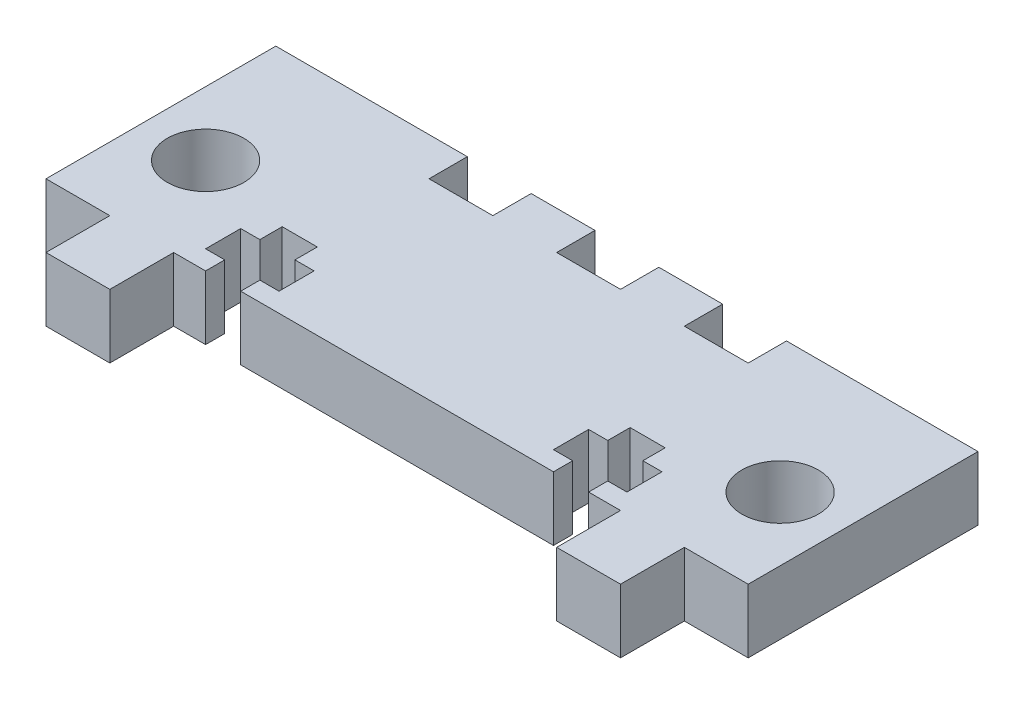
SolidWorks part; units mm, degrees
material "Balsa"
ref_plane "Plan de face" through (0, 0, 0) normal (0, 0, 1) x (1, 0, 0)
ref_plane "Plan de dessus" through (0, 0, 0) normal (0, 1, 0) x (1, 0, 0)
ref_plane "Plan de droite" through (0, 0, 0) normal (1, 0, 0) x (0, 0, -1)
sketch "Esquisse1" plane through (0, 0, 0) normal (0, 1, 0) x (1, 0, 0)
  line L1 (-27.5, 15.5) -> (27.5, 15.5)
  line L2 (-27.5, 15.5) -> (-27.5, -7.5)
  line L3 (-27.5, -7.5) -> (27.5, -7.5)
  line L4 (27.5, 15.5) -> (27.5, -7.5)
  dimension "D1" = 23
  dimension "D2" = 55
  dimension "D3" = 27.5
  dimension "D4" = 7.5
extrude "Boss.-Extru.1" add sketch "Esquisse1" along normal blind 5
sketch "Esquisse2" plane through (0, 5, 0) normal (0, 1, 0) x (1, 0, 0)
  line L1 (27.5, 15.5) -> (-27.5, 15.5) construction
  circle A0 centre (-22.5, 5) radius 3
  circle A1 centre (22.5, 5) radius 3
  dimension "D1" = 6
  dimension "D2" = 6
  dimension "D3" = 45
  dimension "D4" = 22.5
  dimension "D5" = 10.5
extrude "Enlèv. mat.-Extru.1" cut sketch "Esquisse2" against normal blind 5
sketch "Esquisse4" plane through (0, 5, 0) normal (0, 1, 0) x (1, 0, 0)
  line L0 (-15, 3.5) -> (-15, 1.75)
  line L1 (-27.5, -7.5) -> (27.5, -7.5) construction
  line L2 (-15, 1.75) -> (-16.5, 1.75)
  line L3 (-16.5, 1.75) -> (-16.5, -1)
  line L4 (-16.5, -1) -> (-15, -1)
  line L5 (-15, -1) -> (-15, -2.5)
  line L6 (-15, -2.5) -> (-12.25, -2.5)
  line L7 (-12.25, -2.5) -> (-12.25, -1)
  line L8 (-12.25, -1) -> (-10.75, -1)
  line L9 (-10.75, -1) -> (-10.75, 1.75)
  line L10 (-10.75, 1.75) -> (-12.25, 1.75)
  line L11 (-12.25, 1.75) -> (-12.25, 3.5)
  line L12 (-12.25, 3.5) -> (-15, 3.5)
  line L13 (-27.5, 15.5) -> (-27.5, -7.5) construction
  line L14 (0, -4.1132) -> (0, 9.935) construction
  line L15 (12.25, 3.5) -> (15, 3.5)
  line L16 (12.25, 1.75) -> (12.25, 3.5)
  line L17 (10.75, 1.75) -> (12.25, 1.75)
  line L18 (10.75, -1) -> (10.75, 1.75)
  line L19 (12.25, -1) -> (10.75, -1)
  line L20 (12.25, -2.5) -> (12.25, -1)
  line L21 (15, -2.5) -> (12.25, -2.5)
  line L22 (15, -1) -> (15, -2.5)
  line L23 (16.5, -1) -> (15, -1)
  line L24 (16.5, 1.75) -> (16.5, -1)
  line L25 (15, 1.75) -> (16.5, 1.75)
  line L26 (15, 3.5) -> (15, 1.75)
  dimension "D1" = 2.75
  dimension "D2" = 2.75
  dimension "D3" = 1.5
  dimension "D4" = 1.5
  dimension "D5" = 1.5
  dimension "D6" = 1.5
  dimension "D7" = 1.75
  dimension "D8" = 1.75
  dimension "D9" = 2.75
  dimension "D10" = 2.75
  dimension "D11" = 5
  dimension "D12" = 11
extrude "Enlèv. mat.-Extru.2" cut sketch "Esquisse4" against normal blind 10
sketch "Esquisse5" plane through (0, 5, 0) normal (0, 1, 0) x (1, 0, 0)
  line L0 (-27.5, -7.5) -> (27.5, -7.5) construction
  line L2 (-27.5, -7.5) -> (-22.5, -7.5)
  line L3 (-27.5, -7.5) -> (-27.5, -2.5)
  line L4 (-27.5, -2.5) -> (-22.5, -2.5)
  line L7 (-17.5, -7.5) -> (17.5, -7.5)
  line L8 (-17.5, -7.5) -> (-17.5, -2.5)
  line L9 (-17.5, -2.5) -> (17.5, -2.5)
  line L10 (17.5, -7.5) -> (17.5, -2.5)
  line L11 (-22.5, -7.5) -> (-22.5, -2.5)
  line L12 (27.5, -7.5) -> (22.5, -7.5)
  line L13 (27.5, -7.5) -> (27.5, -2.5)
  line L14 (27.5, -2.5) -> (22.5, -2.5)
  line L15 (22.5, -7.5) -> (22.5, -2.5)
  dimension "D1" = 5
  dimension "D2" = 5
  dimension "D3" = 5
  dimension "D4" = 5
  dimension "D5" = 5
  dimension "D6" = 5
  dimension "D9" = 5
extrude "Enlèv. mat.-Extru.3" cut sketch "Esquisse5" against normal through all
sketch "Esquisse7" plane through (0, 5, 0) normal (0, 1, 0) x (1, 0, 0)
  line L0 (27.5, 15.5) -> (-27.5, 15.5) construction
  line L1 (-2.5, 15.5) -> (2.5, 15.5)
  line L2 (-2.5, 15.5) -> (-2.5, 12.5)
  line L3 (-2.5, 12.5) -> (2.5, 12.5)
  line L4 (2.5, 15.5) -> (2.5, 12.5)
  line L6 (7.5, 15.5) -> (12.5, 15.5)
  line L7 (7.5, 15.5) -> (7.5, 12.5)
  line L8 (7.5, 12.5) -> (12.5, 12.5)
  line L9 (12.5, 15.5) -> (12.5, 12.5)
  line L10 (-7.5, 15.5) -> (-12.5, 15.5)
  line L11 (-7.5, 15.5) -> (-7.5, 12.5)
  line L12 (-7.5, 12.5) -> (-12.5, 12.5)
  line L13 (-12.5, 15.5) -> (-12.5, 12.5)
  dimension "D1" = 3
  dimension "D2" = 5
  dimension "D3" = 5
  dimension "D4" = 5
  dimension "D5" = 3
  dimension "D6" = 3
  dimension "D7" = 5
  dimension "D8" = 5
  dimension "D9" = 2.5
extrude "Enlèv. mat.-Extru.4" cut sketch "Esquisse7" against normal through all
